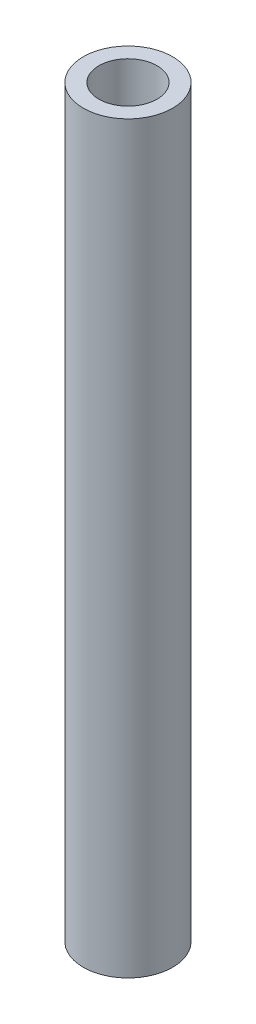
SolidWorks part; units mm, degrees
material "6020 Alloy"
ref_plane "Front Plane" through (0, 0, 0) normal (0, 0, 1) x (1, 0, 0)
ref_plane "Top Plane" through (0, 0, 0) normal (0, 1, 0) x (1, 0, 0)
ref_plane "Right Plane" through (0, 0, 0) normal (1, 0, 0) x (0, 0, -1)
sketch "Sketch1" plane through (0, 0, 0) normal (0, 1, 0) x (1, 0, 0)
  circle A0 centre (0, 0) radius 3.1
  circle A1 centre (0, 0) radius 4.7625
  dimension "D1" = 6.2
  dimension "D2" = 9.525
extrude "Boss-Extrude1" add sketch "Sketch1" along normal blind 79.375 contours A0
